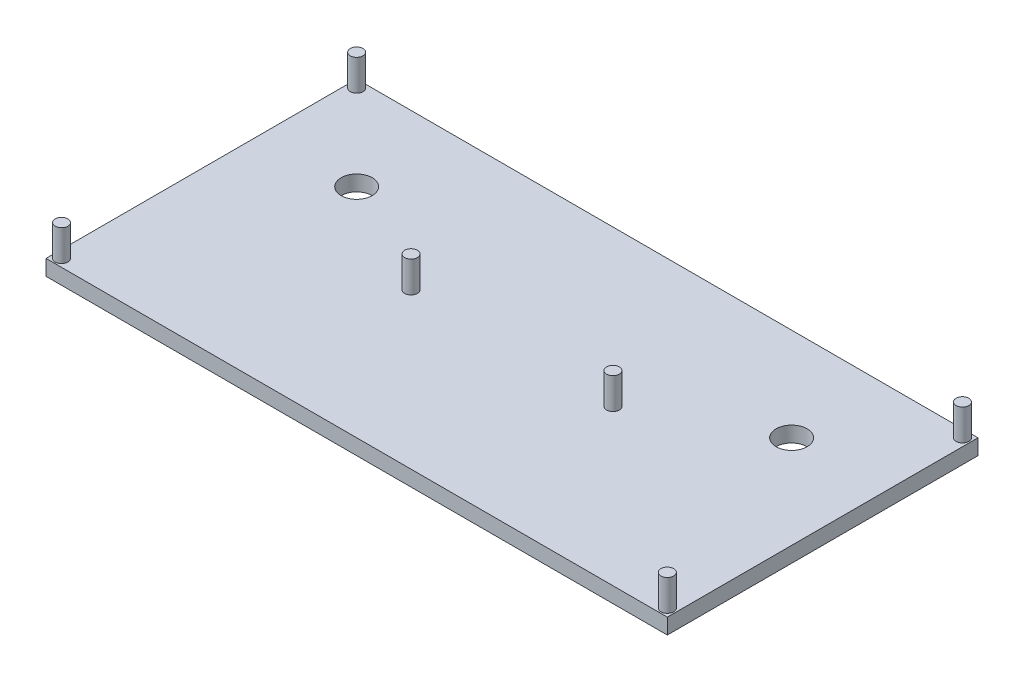
SolidWorks part; units mm, degrees
ref_plane "Front Plane" through (0, 0, 0) normal (0, 0, 1) x (1, 0, 0)
ref_plane "Top Plane" through (0, 0, 0) normal (0, 1, 0) x (1, 0, 0)
ref_plane "Right Plane" through (0, 0, 0) normal (1, 0, 0) x (0, 0, -1)
sketch "Sketch1" plane through (0, 0, 0) normal (0, 1, 0) x (1, 0, 0)
  line L1 (0, 0) -> (200, 0)
  line L2 (0, 0) -> (0, 100)
  line L3 (0, 100) -> (200, 100)
  line L4 (200, 0) -> (200, 100)
  dimension "D1" = 200
  dimension "D2" = 100
extrude "Boss-Extrude1" add sketch "Sketch1" along normal blind 5
sketch "Sketch2" plane through (0, 5, 0) normal (0, 1, 0) x (1, 0, 0)
  line L0 (0, 50) -> (200, 50) construction
  line L1 (0, 100) -> (0, 0) construction
  line L2 (200, 0) -> (200, 100) construction
  line L3 (100, 100) -> (100, 0) construction
  line L4 (200, 100) -> (0, 100) construction
  line L5 (0, 0) -> (200, 0) construction
  circle A0 centre (2.5, 97.5) radius 2.05
  circle A1 centre (197.5, 97.5) radius 2.05
  circle A2 centre (197.5, 2.5) radius 2.05
  circle A3 centre (2.5, 2.5) radius 2.05
  circle A4 centre (67.5, 50) radius 2.05
  circle A5 centre (132.5, 50) radius 2.05
  dimension "D1" = 4.1
  dimension "D4" = 4.1
  dimension "D2" = 2.5
  dimension "D3" = 2.5
  dimension "D5" = 67.5
extrude "Boss-Extrude2" add sketch "Sketch2" along normal blind 10
sketch "Sketch3" plane through (0, 0, 0) normal (0, -1, 0) x (-1, 0, 0)
  line L0 (-200, 0) -> (-200, 100) construction
  line L1 (-200, 100) -> (0, 100) construction
  line L2 (-100, 100) -> (-100, 0) construction
  line L3 (0, 0) -> (-200, 0) construction
  circle A0 centre (-170, 70) radius 5
  circle A1 centre (-30, 70) radius 5
  dimension "D3" = 10
  dimension "D1" = 30
  dimension "D2" = 30
extrude "Cut-Extrude1" cut sketch "Sketch3" against normal blind 10
